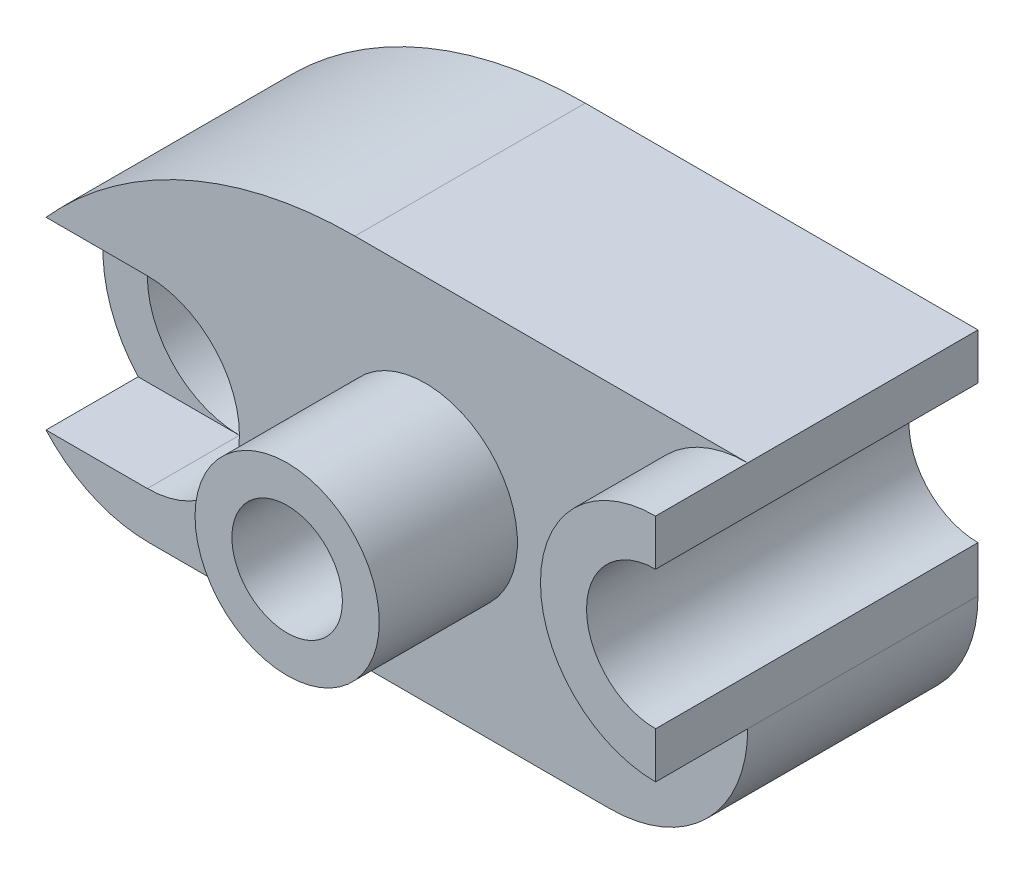
SolidWorks part; units mm, degrees
ref_plane "Front Plane" through (0, 0, 0) normal (0, 0, 1) x (1, 0, 0)
ref_plane "Top Plane" through (0, 0, 0) normal (0, 1, 0) x (1, 0, 0)
ref_plane "Right Plane" through (0, 0, 0) normal (1, 0, 0) x (0, 0, -1)
sketch "Sketch1" plane through (0, 0, 0) normal (0, 0, 1) x (1, 0, 0)
  line L1 (0, 0) -> (160, 0)
  line L2 (0, 0) -> (0, 80)
  line L3 (0, 80) -> (160, 80)
  line L4 (160, 0) -> (160, 80)
  dimension "D1" = 160
  dimension "D2" = 80
extrude "Boss-Extrude1" add sketch "Sketch1" along normal blind 90
sketch "Sketch2" plane through (0, 0, 90) normal (0, 0, 1) x (1, 0, 0)
  line L0 (160, 0) -> (160, 80) construction
  line L1 (0, 0) -> (160, 0) construction
  line L2 (130, 0) -> (160, 0)
  line L3 (160, 0) -> (160, 30)
  line L4 (160, 70) -> (160, 40)
  arc A0 (160, 70) -> (160, 40) centre (160, 55) ccw
  arc A1 (160, 80) -> (160, 30) centre (160, 55) ccw
  arc A2 (160, 30) -> (130, 0) centre (130, 30) cw
  line M2 (0, 0) -> (160, 0)
  line M3 (160, 0) -> (160, 80)
  dimension "D1" = 30
  dimension "D4" = 15
  dimension "D5" = 25
  dimension "D2" = 30
  dimension "D3" = 30
  dimension "D6" = 0
extrude "Cut-Extrude1" cut sketch "Sketch2" against normal blind 90 contours A0 M3 | A2 M3 M2
sketch "Sketch3" plane through (0, 0, 90) normal (0, 0, 1) x (1, 0, 0)
  line L0 (0, 80) -> (0, 0) construction
  line L1 (0, 30) -> (0, 0)
  line L2 (0, 0) -> (30, 0)
  arc A0 (0, 30) -> (30, 0) centre (30, 30) ccw
  dimension "D1" = 30
  dimension "D2" = 30
  dimension "D3" = 30
  dimension "D4" = 0
extrude "Cut-Extrude2" cut sketch "Sketch3" against normal blind 90
sketch "Sketch4" plane through (0, 0, 0) normal (-1, 0, 0) x (0, 0, 1)
  line L0 (0, 80) -> (0, 30) construction
  line L1 (0, 65) -> (10, 65)
  line L2 (0, 65) -> (0, 15)
  line L3 (0, 15) -> (10, 15)
  line L4 (10, 65) -> (10, 15)
  line L5 (90, 80) -> (0, 80) construction
  line L6 (0, 65) -> (10, 65)
  line L7 (0, 65) -> (0, 80)
  line L8 (0, 80) -> (10, 80)
  line L9 (10, 65) -> (10, 80)
  line L11 (0, 15) -> (10, 15)
  line L12 (0, 15) -> (0, 0)
  line L13 (0, 0) -> (10, 0)
  line L14 (10, 15) -> (10, 0)
  line M3 (90, 80) -> (0, 80)
  line M4 (0, 80) -> (0, 30)
  dimension "D1" = 10
  dimension "D2" = 15
  dimension "D3" = 50
  dimension "D4" = 15
extrude "Cut-Extrude3" cut sketch "Sketch4" against normal blind 215 contours L1 L9 M3 M4 | L14 L3 L12 L13
sketch "Sketch5" plane through (0, 0, 0) normal (0, 0, -1) x (-1, 0, 0)
  line L0 (0, 80) -> (0, 30) construction
  line L1 (-160, 80) -> (0, 80) construction
  line L2 (-90, 65) -> (0, 65)
  line L3 (0, 65) -> (0, 30)
  line L4 (-90, 65) -> (-148.8197, 65)
  line L5 (-4.0192, 15) -> (-155.9808, 15)
  line L6 (-160, 40) -> (-160, 30)
  circle A0 centre (-90, 40) radius 25
  arc A1 (-160, 30) -> (-155.9808, 15) centre (-130, 30) ccw
  arc A2 (-160, 30) -> (-155.9808, 15) centre (-130, 30) ccw construction
  arc A3 (-148.8197, 65) -> (-160, 40) centre (-160, 55) cw
  arc A4 (0, 30) -> (-4.0192, 15) centre (-30, 30) cw
  arc A5 (-4.0192, 15) -> (0, 30) centre (-30, 30) ccw construction
  arc M1 (-160, 30) -> (-155.9808, 15) centre (-130, 30) ccw
  line M2 (-155.9808, 15) -> (-4.0192, 15)
  arc M3 (-4.0192, 15) -> (0, 30) centre (-30, 30) ccw
  line M4 (0, 30) -> (0, 65)
  line M5 (0, 65) -> (-148.8197, 65)
  arc M6 (-148.8197, 65) -> (-160, 40) centre (-160, 55) cw
  line M7 (-160, 40) -> (-160, 30)
  dimension "D1" = 50
  dimension "D4" = 15
  dimension "D2" = 90
  dimension "D3" = 40
  dimension "D5" = 58.8197
  dimension "D6" = 90
extrude "Cut-Extrude4" cut sketch "Sketch5" against normal blind 10 contours A0 M5 M6 M7 M1 M2 | A0 L5 M3 M4 M5
sketch "Sketch6" plane through (0, 0, 90) normal (0, 0, 1) x (1, 0, 0)
  line L1 (160, 80) -> (0, 80) construction
  line L2 (0, 30) -> (0, 80)
  line L3 (0, 80) -> (74.7214, 80)
  arc A0 (0, 30) -> (7.6393, 50) centre (30, 30) cw
  arc A2 (7.6393, 50) -> (74.7214, 80) centre (74.7214, -10) cw
  dimension "D1" = 30
  dimension "D2" = 30
  dimension "D3" = 20
extrude "Cut-Extrude6" cut sketch "Sketch6" against normal blind 263
ref_plane "Plane1" through (0, 0, 60) normal (0, 0, 1) x (1, 0, 0)
sketch "Sketch7" plane through (0, 0, 60) normal (0, 0, 1) x (1, 0, 0)
  line L1 (160, 80) -> (0, 80)
  line L2 (160, 80) -> (160, 0)
  line L3 (160, 0) -> (0, 0)
  line L4 (0, 80) -> (0, 0)
  dimension "D1" = 160
  dimension "D2" = 80
extrude "Cut-Extrude7" cut sketch "Sketch7" along normal blind 263
sketch "Sketch8" plane through (0, 0, 60) normal (0, 0, 1) x (1, 0, 0)
  line L0 (30, 0) -> (130, 0) construction
  circle A0 centre (90, 40) radius 20
  dimension "D1" = 40
  dimension "D2" = 40
  dimension "D3" = 70
extrude "Boss-Extrude2" add sketch "Sketch8" along normal blind 30
sketch "Sketch9" plane through (0, 0, 90) normal (0, 0, 1) x (1, 0, 0)
  circle A0 centre (90, 40) radius 11
  dimension "D1" = 22
extrude "Cut-Extrude8" cut sketch "Sketch9" against normal blind 117
sketch "Sketch10" plane through (0, 0, 60) normal (0, 0, 1) x (1, 0, 0)
  line L0 (160, 30) -> (160, 40) construction
  line L1 (160, 40) -> (160, 30)
  line L2 (160, 70) -> (160, 80)
  arc A0 (160, 80) -> (160, 30) centre (160, 55) ccw
  arc A1 (130, 0) -> (160, 30) centre (130, 30) ccw construction
  arc A2 (160, 70) -> (160, 40) centre (160, 55) ccw
extrude "Boss-Extrude3" add sketch "Sketch10" along normal blind 20
sketch "Sketch11" plane through (0, 0, 60) normal (0, 0, 1) x (1, 0, 0)
  line L0 (29.6393, 50) -> (7.6393, 50)
  line L1 (29.6393, 10) -> (7.6393, 10)
  line L2 (30, 0) -> (130, 0) construction
  circle A0 centre (29.6393, 30) radius 20
  arc A1 (7.6393, 50) -> (30, 0) centre (30, 30) ccw
  arc A2 (7.6393, 50) -> (30, 0) centre (30, 30) ccw construction
  arc M5 (7.6393, 50) -> (30, 0) centre (30, 30) ccw
  dimension "D1" = 22
  dimension "D2" = 22
  dimension "D3" = 10
  dimension "D4" = 10
  dimension "D5" = 50
extrude "Cut-Extrude9" cut sketch "Sketch11" against normal blind 20 contours A0 L0 L1 M5
sketch "Sketch12" plane through (0, 0, 60) normal (0, 0, 1) x (1, 0, 0)
  circle A0 centre (29.6393, 30) radius 20
extrude "Cut-Extrude10" cut sketch "Sketch12" against normal blind 40
sketch "Sketch13" plane through (0, 0, 20) normal (0, 0, 1) x (1, 0, 0)
  circle A0 centre (29.6393, 30) radius 10
  dimension "D1" = 20
extrude "Cut-Extrude11" cut sketch "Sketch13" against normal blind 40
sketch "Sketch14" plane through (0, 0, 90) normal (0, 0, 1) x (1, 0, 0)
  circle A0 centre (90, 40) radius 12
  dimension "D1" = 24
extrude "Cut-Extrude12" cut sketch "Sketch14" against normal blind 114
